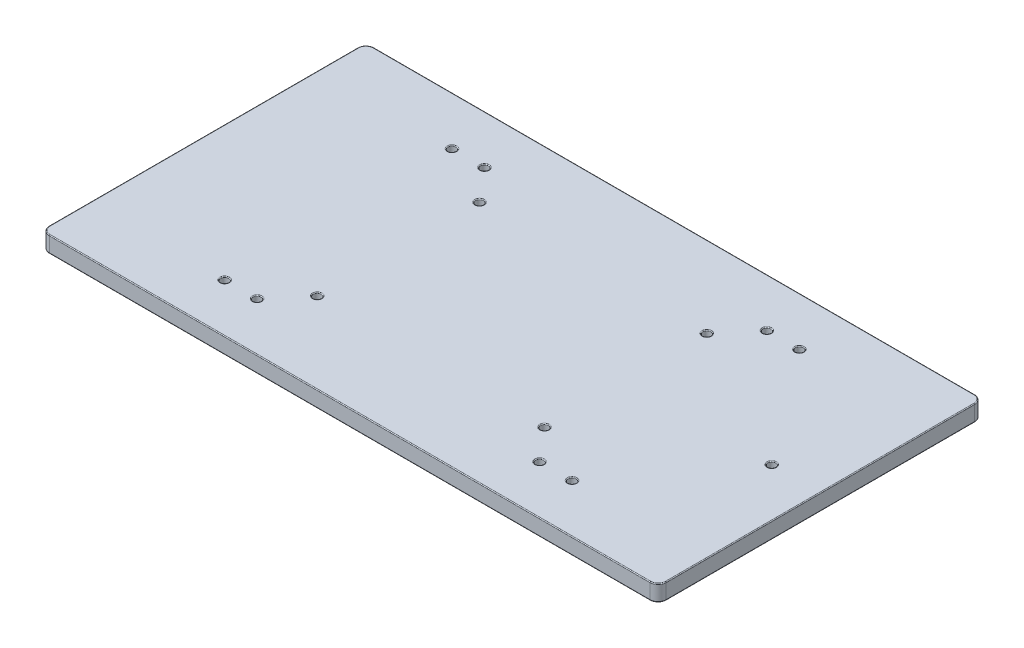
SolidWorks part; units mm, degrees
ref_plane "Front Plane" through (0, 0, 0) normal (0, 0, 1) x (1, 0, 0)
ref_plane "Top Plane" through (0, 0, 0) normal (0, 1, 0) x (1, 0, 0)
ref_plane "Right Plane" through (0, 0, 0) normal (1, 0, 0) x (0, 0, -1)
sketch "Sketch1" plane through (0, 0, 0) normal (0, 1, 0) x (1, 0, 0)
  line L0 (80, 50) -> (80, -50) construction
  line L1 (-95, 50) -> (95, 50)
  line L2 (-95, 50) -> (-95, -50)
  line L3 (-95, -50) -> (95, -50)
  line L4 (95, 50) -> (95, -50)
  line L5 (-95, 50) -> (95, -50) construction
  line L6 (-95, -50) -> (95, 50) construction
  line L7 (-35, 25) -> (35, 25) construction
  line L8 (-35, 25) -> (-35, -25) construction
  line L9 (-35, -25) -> (35, -25) construction
  line L10 (35, 25) -> (35, -25) construction
  line L11 (-35, 25) -> (35, -25) construction
  line L12 (-35, -25) -> (35, 25) construction
  line L13 (0, 17.8351) -> (0, 0) construction
  line L14 (0, 0) -> (29.8844, 0) construction
  circle A0 centre (-35, 25) radius 1.25
  circle A1 centre (35, 25) radius 1.25
  circle A2 centre (35, -25) radius 1.25
  circle A3 centre (-35, -25) radius 1.25
  circle A4 centre (80, 0) radius 1.25
  circle A5 centre (-53.5, -35) radius 1.25
  circle A6 centre (-43.5, -35) radius 1.25
  circle A7 centre (-53.5, 35) radius 1.25
  circle A8 centre (-43.5, 35) radius 1.25
  circle A9 centre (53.5, -35) radius 1.25
  circle A10 centre (43.5, -35) radius 1.25
  circle A11 centre (53.5, 35) radius 1.25
  circle A12 centre (43.5, 35) radius 1.25
  point P0 (0, 0)
  point P5 (0, 0)
  dimension "D1" = 190
  dimension "D5" = 2.5
  dimension "D6" = 2.5
  dimension "D8" = 43.5
  dimension "D11" = 2.5
  dimension "D2" = 100
  dimension "D3" = 70
  dimension "D4" = 50
  dimension "D7" = 15
  dimension "D9" = 10
  dimension "D10" = 15
extrude "Boss-Extrude1" add sketch "Sketch1" along normal blind 5
fillet "Fillet1" radius 2.5 4 edges at (-95, 2.5, -50) (-95, 2.5, 50) (95, 2.5, -50) (95, 2.5, 50)
fillet "Fillet2" radius 0.25 42 edges at (43.5, 0, -33.75) (53.5, 0, -33.75) (43.5, 0, 33.75) (53.5, 0, 33.75) (-43.5, 0, -36.25) (-53.5, 0, -36.25) (-43.5, 0, 36.25) (-53.5, 0, 36.25) (80, 0, 1.25) (-35, 0, 26.25) (35, 0, 26.25) (35, 0, -23.75) (-35, 0, -23.75) (-94.2678, 0, 49.2678) (0, 0, 50) (94.2678, 0, 49.2678) (95, 0, 0) (94.2678, 0, -49.2678) (0, 0, -50) (-94.2678, 0, -49.2678) (-95, 0, 0) (43.5, 5, -33.75) (43.5, 5, 33.75) (-43.5, 5, -36.25) (-43.5, 5, 36.25) (80, 5, 1.25) (35, 5, 26.25) (-35, 5, -23.75) (94.2678, 5, -49.2678) (95, 5, 0) (94.2678, 5, 49.2678) (0, 5, 50) (-94.2678, 5, 49.2678) (-95, 5, 0) (-94.2678, 5, -49.2678) (0, 5, -50) (35, 5, -23.75) (-35, 5, 26.25) (-53.5, 5, 36.25) (-53.5, 5, -36.25) (53.5, 5, 33.75) (53.5, 5, -33.75)
